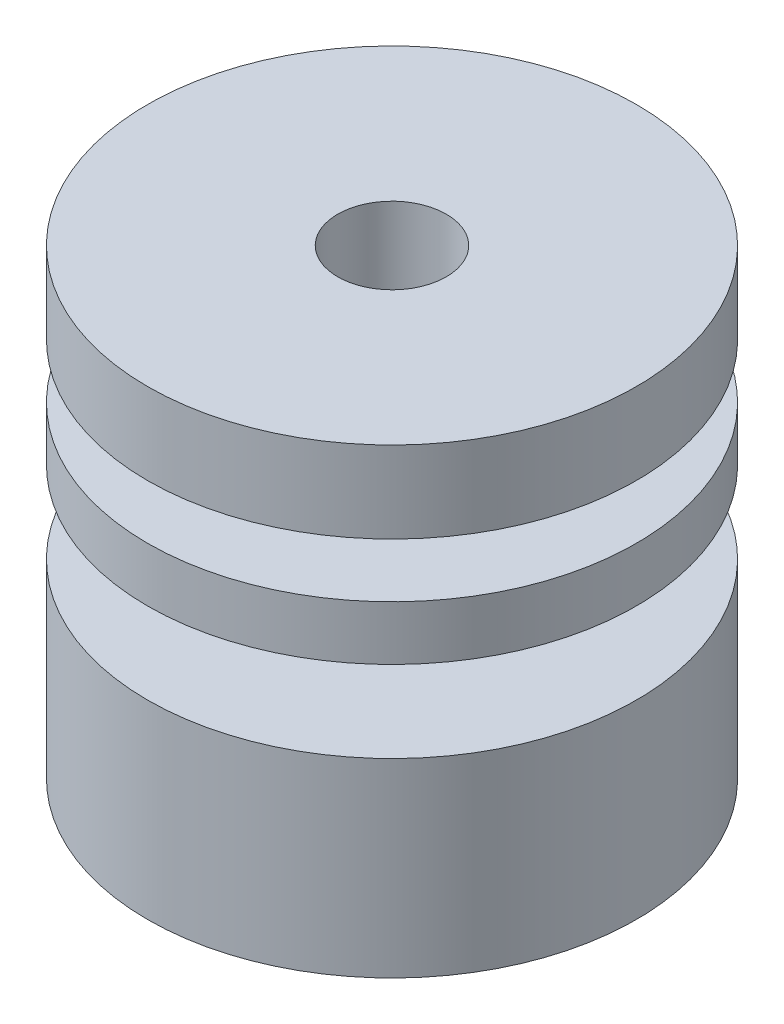
SolidWorks part; units mm, degrees
ref_plane "Front Plane" through (0, 0, 0) normal (0, 0, 1) x (1, 0, 0)
ref_plane "Top Plane" through (0, 0, 0) normal (0, 1, 0) x (1, 0, 0)
ref_plane "Right Plane" through (0, 0, 0) normal (1, 0, 0) x (0, 0, -1)
sketch "Sketch1" plane through (0, 0, 0) normal (0, 0, 1) x (1, 0, 0)
  line L1 (0, 0) -> (2.5, 0) construction
  line L2 (0, 0) -> (0, 17) construction
  line L3 (0, 17) -> (2.5, 17) construction
  line L4 (2.5, 0) -> (2.5, 17) construction
  line L5 (2.5, 0) -> (9, 0)
  line L6 (2.5, 0) -> (2.5, 7)
  line L7 (2.5, 7) -> (9, 7)
  line L8 (9, 0) -> (9, 7)
  line L9 (2.5, 10) -> (9, 10)
  line L10 (2.5, 10) -> (2.5, 12)
  line L11 (2.5, 12) -> (9, 12)
  line L12 (9, 10) -> (9, 12)
  line L13 (2.5, 17) -> (9, 17)
  line L14 (2.5, 17) -> (2.5, 14)
  line L15 (2.5, 14) -> (9, 14)
  line L16 (9, 17) -> (9, 14)
  line L17 (2.5, 17) -> (2, 17)
  line L18 (2.5, 17) -> (2.5, 0)
  line L19 (2.5, 0) -> (2, 0)
  line L20 (2, 17) -> (2, 0)
  line L21 (2.5, 14) -> (4.5, 14)
  line L22 (2.5, 14) -> (2.5, 12)
  line L23 (2.5, 12) -> (4.5, 12)
  line L24 (4.5, 14) -> (4.5, 12)
  line L25 (2.5, 10) -> (4.5, 10)
  line L26 (2.5, 10) -> (2.5, 7)
  line L27 (2.5, 7) -> (4.5, 7)
  line L28 (4.5, 10) -> (4.5, 7)
  dimension "D1" = 17
  dimension "D2" = 2.5
  dimension "D3" = 7
  dimension "D4" = 9
  dimension "D5" = 2
  dimension "D6" = 3
  dimension "D7" = 3
  dimension "D8" = 0.5
  dimension "D9" = 2
revolve "Revolve1" add sketch "Sketch1" angle 360 about L2
